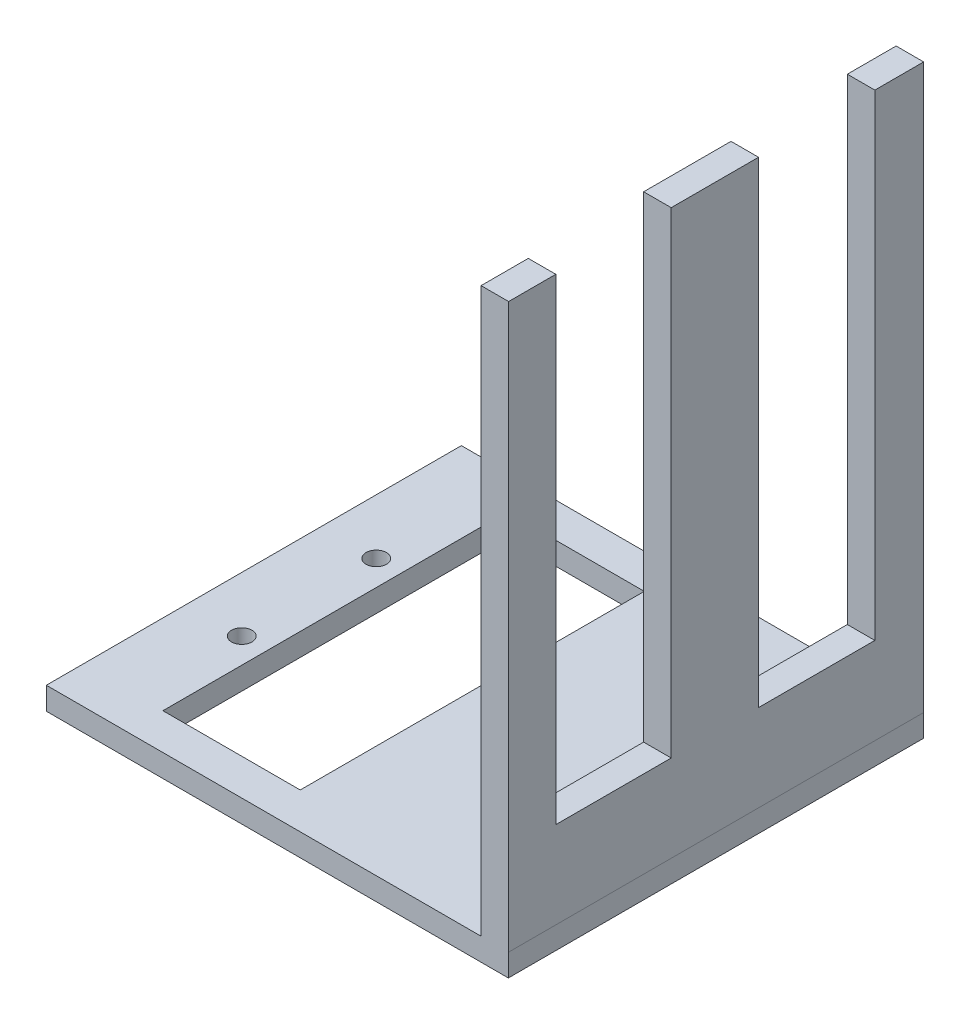
SolidWorks part; units mm, degrees
ref_plane "Front Plane" through (0, 0, 0) normal (0, 0, 1) x (1, 0, 0)
ref_plane "Top Plane" through (0, 0, 0) normal (0, 1, 0) x (1, 0, 0)
ref_plane "Right Plane" through (0, 0, 0) normal (1, 0, 0) x (0, 0, -1)
sketch "Sketch1" plane through (0, 0, 0) normal (0, 1, 0) x (1, 0, 0)
  line L1 (-40.3324, 34.6721) -> (41.6676, 34.6721)
  line L2 (-40.3324, 34.6721) -> (-40.3324, -38.9879)
  line L3 (-40.3324, -38.9879) -> (41.6676, -38.9879)
  line L4 (41.6676, 34.6721) -> (41.6676, -38.9879)
extrude "Boss-Extrude1" add sketch "Sketch1" along normal blind 4
sketch "Sketch2" plane through (0, 4, 0) normal (0, 1, 0) x (1, 0, 0)
  line L1 (36.8283, 34.6721) -> (41.7155, 34.6721)
  line L2 (36.8283, 34.6721) -> (36.8283, -38.9879)
  line L3 (36.8283, -38.9879) -> (41.7155, -38.9879)
  line L4 (41.7155, 34.6721) -> (41.7155, -38.9879)
  line L5 (41.6676, 34.6721) -> (-40.3324, 34.6721) construction
extrude "Boss-Extrude2" add sketch "Sketch2" along normal blind 100
sketch "Sketch3" plane through (0, 4, 0) normal (0, 1, 0) x (1, 0, 0)
  line L0 (-30.5441, -2.1579) -> (-30.5441, -14.0979) construction
  line L1 (-40.2041, 34.6721) -> (-40.2041, -38.9879) construction
  line L2 (36.8283, 34.6721) -> (-40.3324, 34.6721) construction
  line L3 (-40.3324, -38.9879) -> (36.8283, -38.9879) construction
  line L4 (-40.2041, -2.1579) -> (-30.5441, -2.1579) construction
  line L5 (-30.5441, -2.1579) -> (-30.5441, 9.7821) construction
  circle A0 centre (-30.5441, 9.7821) radius 1.8125
  circle A1 centre (-30.5441, -14.0979) radius 1.8125
extrude "Cut-Extrude1" cut sketch "Sketch3" against normal blind 10
sketch "Sketch4" plane through (0, 4, 0) normal (0, 1, 0) x (1, 0, 0)
  line L1 (-1.7001, 28.5027) -> (-26.0701, 28.5027)
  line L2 (-1.7001, 28.5027) -> (-1.7001, -32.56)
  line L3 (-1.7001, -32.56) -> (-26.0701, -32.56)
  line L4 (-26.0701, 28.5027) -> (-26.0701, -32.56)
extrude "Cut-Extrude2" cut sketch "Sketch4" against normal blind 10
sketch "Sketch5" plane through (41.7155, 0, 0) normal (1, 0, 0) x (0, 0, -1)
  line L1 (26.0087, 19.4117) -> (5.3661, 19.4117)
  line L2 (26.0087, 19.4117) -> (26.0087, 120.5415)
  line L3 (26.0087, 120.5415) -> (5.3661, 120.5415)
  line L4 (5.3661, 19.4117) -> (5.3661, 120.5415)
  line L5 (-10.1358, 19.4117) -> (-30.6149, 19.4117)
  line L6 (-10.1358, 19.4117) -> (-10.1358, 119.592)
  line L7 (-10.1358, 119.592) -> (-30.6149, 119.592)
  line L8 (-30.6149, 19.4117) -> (-30.6149, 119.592)
extrude "Cut-Extrude3" cut sketch "Sketch5" against normal blind 10
